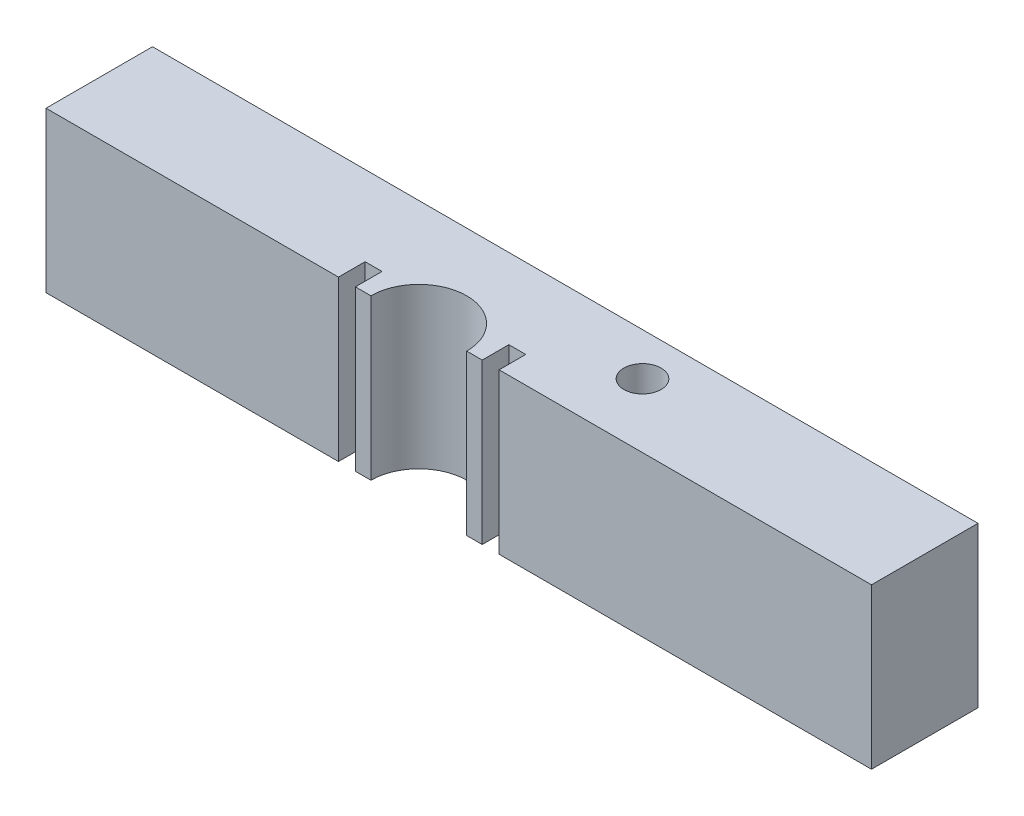
SolidWorks part; units mm, degrees
ref_plane "Front" through (0, 0, 0) normal (0, 0, 1) x (1, 0, 0)
ref_plane "Top" through (0, 0, 0) normal (0, 1, 0) x (1, 0, 0)
ref_plane "Right" through (0, 0, 0) normal (1, 0, 0) x (0, 0, -1)
sketch "Sketch1" plane through (0, 0, 0) normal (0, 1, 0) x (1, 0, 0)
  line L1 (-70, 20) -> (85, 20)
  line L2 (-70, 20) -> (-70, -20)
  line L3 (-70, -20) -> (85, -20)
  line L4 (85, 20) -> (85, -20)
  circle A0 centre (0, 0) radius 9
  point P8 (-70, 0)
  dimension "D1" = 18
  dimension "D2" = 40
  dimension "D3" = 155
  dimension "D4" = 70
extrude "Boss-Extrude1" add sketch "Sketch1" along normal blind 30
ref_plane "Plane1" through (0, 0, 0) normal (0, 0, 1) x (1, 0, 0)
sketch "Sketch3" plane through (0, 30, 0) normal (0, 1, 0) x (1, 0, 0)
  line L0 (-11.9063, 5) -> (-11.9063, -5)
  line L3 (11.9062, 5) -> (11.9062, -5)
  line L5 (-11.9063, 5) -> (-15.0813, 5)
  line L6 (-11.9063, 5) -> (-11.9063, -5)
  line L7 (-11.9063, -5) -> (-15.0813, -5)
  line L8 (-15.0813, 5) -> (-15.0813, -5)
  line L9 (11.9062, 5) -> (15.0812, 5)
  line L10 (11.9062, 5) -> (11.9062, -5)
  line L11 (11.9062, -5) -> (15.0812, -5)
  line L12 (15.0812, 5) -> (15.0812, -5)
  line L13 (-70, 0) -> (85, 0) construction
  line L14 (-70, 20) -> (-70, -20) construction
  line L15 (85, -20) -> (85, 20) construction
  circle A0 centre (0, 0) radius 9 construction
  circle A1 centre (0, 0) radius 9
  circle A3 centre (0, 0) radius 11.9062
  point P6 (-15.0813, 0)
  point P19 (15.0812, 0)
  line M3 (-70, -20) -> (85, -20)
  line M5 (85, 20) -> (-70, 20)
  dimension "D1" = 23.8125
  dimension "D2" = 3.175
  dimension "D3" = 10
extrude "Cut-Extrude2" cut sketch "Sketch3" against normal through all contours L8 L6 L0 M5 M3 | L12 L3 L10 M5 M3 | L13 L8 L7 L6 | L13 L10 L11 L12
sketch "Sketch2" plane through (0, 0, 0) normal (0, 0, 1) x (1, 0, 0)
  line L4 (-70, 0) -> (85, 0)
  line L5 (85, 0) -> (85, 30)
  line L6 (85, 30) -> (-70, 30)
  line L7 (-70, 30) -> (-70, 0)
  line L8 (-70, 0) -> (85, 0)
  line L9 (85, 0) -> (85, 30)
  line L10 (85, 30) -> (-70, 30)
  line L11 (-70, 30) -> (-70, 0)
  dimension "D1" = 0
extrude "Cut-Extrude1" cut sketch "Sketch2" along normal through all
sketch "Sketch4" plane through (0, 0, 0) normal (0, -1, 0) x (1, 0, 0)
  line L1 (85, -20) -> (-70, -20) construction
  circle A1 centre (30, -12) radius 3.5
  dimension "D1" = 7
  dimension "D3" = 8
  dimension "D4" = 30
extrude "Cut-Extrude3" cut sketch "Sketch4" against normal through all
equation "\"Length\"= 155mm'Match working Model"
equation "\"D3@Sketch1\"= \"Length\""
equation "\"ΔTCPC\"= 30mm'Between 0-5cm (Working Models should have minimum of 2cm already to reach the 2-7cm ΔTCPC specifications )in 0.5cm increments"
equation "\"D1@Boss-Extrude1\" = \"ΔTCPC\""
equation "\"Width\"= 40.00mm'Match working Model"
equation "\"D2@Sketch1\"=\"Width\""
